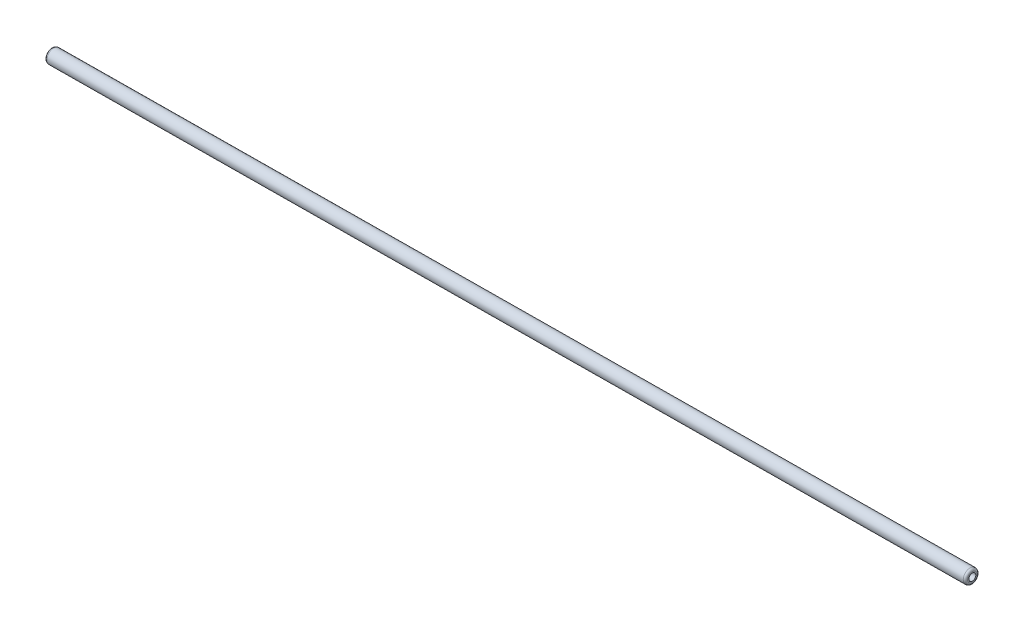
SolidWorks part; units mm, degrees
material "Alloy Steel"
ref_plane "Front Plane" through (0, 0, 0) normal (0, 0, 1) x (1, 0, 0)
ref_plane "Top Plane" through (0, 0, 0) normal (0, 1, 0) x (1, 0, 0)
ref_plane "Right Plane" through (0, 0, 0) normal (1, 0, 0) x (0, 0, -1)
sketch "스케치1" plane through (0, 0, 0) normal (0, 1, 0) x (1, 0, 0)
  circle A0 centre (0, 0) radius 7.9375
  circle A1 centre (0, 0) radius 3.975
  dimension "D1" = 15.875
  dimension "D2" = 7.95
extrude "보스-돌출1" add sketch "스케치1" along normal mid plane 1054.1
fillet "필렛1" radius 2.5 2 edges at (0, 527.05, 7.9375) (0, -527.05, 7.9375)
sketch "스케치4" plane through (0, 0, 0) normal (1, 0, 0) x (0, 0, -1)
  line L0 (7.9375, -524.55) -> (7.9375, 524.55) construction
  line L1 (7.9375, -524.55) -> (7.9375, 524.55) construction
  line L2 (-7.9375, 524.55) -> (-7.9375, -524.55) construction
  line L3 (-7.9375, 524.55) -> (-7.9375, -524.55) construction
  line L4 (-5.4375, -527.05) -> (5.4375, -527.05) construction
  line L5 (-5.4375, -527.05) -> (5.4375, -527.05) construction
  line L6 (5.4375, 527.05) -> (-5.4375, 527.05) construction
  line L7 (5.4375, 527.05) -> (-5.4375, 527.05) construction
  line L8 (0, 527.05) -> (0, 0) construction
  line L9 (-213.5443, 263.525) -> (259.7387, 263.525) construction
  line L10 (-81.4653, 263.525) -> (-81.4653, 1052.8) construction
  line L11 (-81.4653, 263.525) -> (-81.4653, 0) construction
  circle A0 centre (0, -497.05) radius 2.5
  circle A1 centre (0, 263.525) radius 2.5 construction
  circle A2 centre (0, 789.925) radius 2.5 construction
  circle A3 centre (0, 263.525) radius 2.5 construction
  circle A4 centre (0, 338.525) radius 2.5
  circle A5 centre (0, 313.525) radius 2.5
  circle A6 centre (0, 814.925) radius 2.5
  dimension "D1" = 5
  dimension "D2" = 5
  dimension "D3" = 5
  dimension "D4" = 5
  dimension "D6" = 5
  dimension "D8" = 5
  dimension "D10" = 5
  dimension "D5" = 30
  dimension "D7" = 75
  dimension "D9" = 50
  dimension "D11" = 25
move or copy body "바디-이동/복사1" bodies to move or copy 101 copy no rotation origin (0, 0, 0) rotation axis (0, 0, 1) rotation angle 90.5
